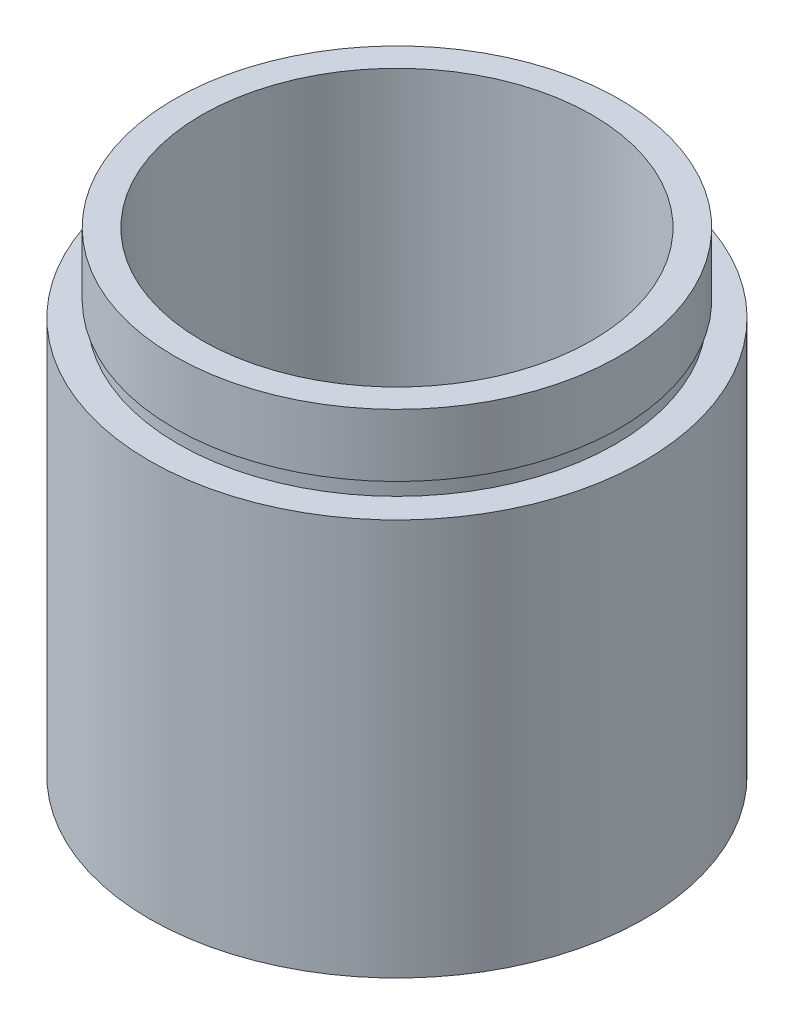
SolidWorks part; units mm, degrees
ref_plane "前视基准面" through (0, 0, 0) normal (0, 0, 1) x (1, 0, 0)
ref_plane "上视基准面" through (0, 0, 0) normal (0, 1, 0) x (1, 0, 0)
ref_plane "右视基准面" through (0, 0, 0) normal (1, 0, 0) x (0, 0, -1)
sketch "草图1" plane through (0, 0, 0) normal (0, 0, 1) x (1, 0, 0)
  line L0 (0, 161.3762) -> (0, 0) construction
  line L1 (141.7365, 0) -> (-131.7984, 0) construction
  line L2 (14.25, 0) -> (14.25, 4.5)
  line L3 (15.85, 0) -> (15.85, 25.4)
  line L4 (14.25, 0) -> (15.85, 0)
  line L5 (14.35, 4.5) -> (14.35, 5.5)
  line L6 (14.25, 4.5) -> (14.35, 4.5)
  line L7 (12.5, 5.5) -> (12.5, 30.4)
  line L8 (12.5, 5.5) -> (14.35, 5.5)
  line L9 (14.25, 30.4) -> (14.25, 26.4)
  line L10 (12.5, 30.4) -> (14.25, 30.4)
  line L11 (14, 26.4) -> (14, 25.4)
  line L12 (14, 26.4) -> (14.25, 26.4)
  line L13 (14, 25.4) -> (15.85, 25.4)
  point P7 (14.25, 2.25)
  dimension "D1" = 14.25
  dimension "D2" = 4.5
  dimension "D3" = 15.85
  dimension "D4" = 14.35
  dimension "D5" = 12.5
  dimension "D6" = 1
  dimension "D7" = 25.4
  dimension "D8" = 14.25
  dimension "D9" = 14
  dimension "D10" = 5
  dimension "D11" = 1
revolve "旋转1" add sketch "草图1" angle 360 about L0
cosmetic thread "装饰螺纹线1"
cosmetic thread "装饰螺纹线2"
cosmetic thread "装饰螺纹线3"
